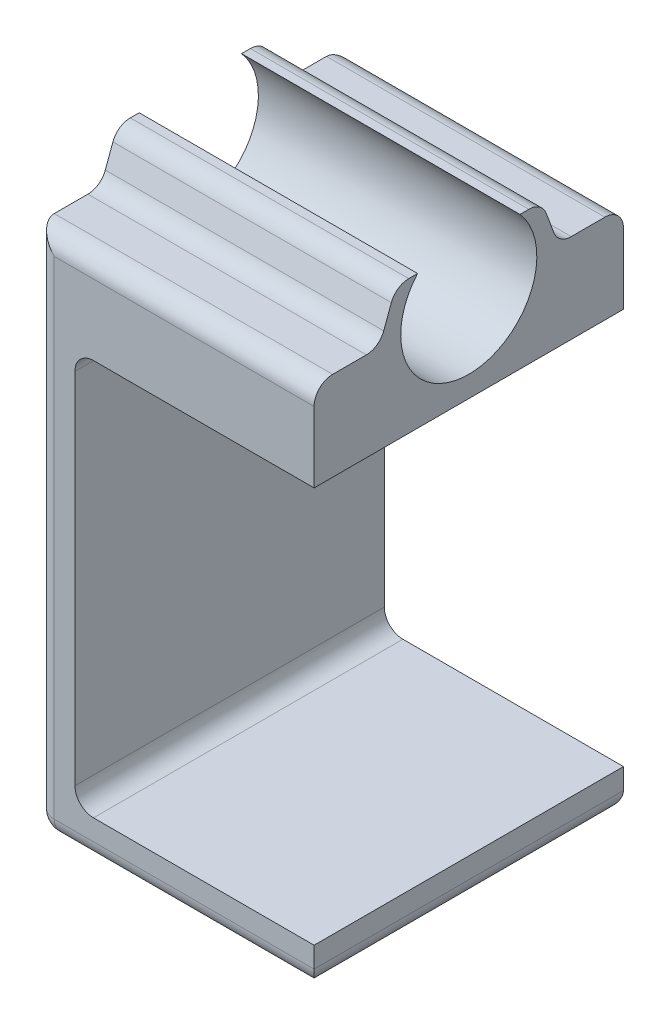
SolidWorks part; units mm, degrees
ref_plane "Front Plane" through (0, 0, 0) normal (0, 0, 1) x (1, 0, 0)
ref_plane "Top Plane" through (0, 0, 0) normal (0, 1, 0) x (1, 0, 0)
ref_plane "Right Plane" through (0, 0, 0) normal (1, 0, 0) x (0, 0, -1)
sketch "Sketch1" plane through (0, 0, 0) normal (0, 1, 0) x (1, 0, 0)
  line L1 (-22.5, -25) -> (22.5, -25)
  line L2 (-22.5, -25) -> (-22.5, 25)
  line L3 (-22.5, 25) -> (22.5, 25)
  line L4 (22.5, -25) -> (22.5, 25)
  line L5 (-22.5, -25) -> (22.5, 25) construction
  line L6 (-22.5, 25) -> (22.5, -25) construction
  point P0 (0, 0)
  dimension "D1" = 45
  dimension "D2" = 50
extrude "Boss-Extrude1" add sketch "Sketch1" along normal blind 92
sketch "Sketch2" plane through (0, 0, -25) normal (0, 0, -1) x (-1, 0, 0)
  line L0 (-22.5, 92) -> (-22.5, 0) construction
  line L1 (-22.5, 6.35) -> (16.15, 6.35)
  line L2 (-22.5, 6.35) -> (-22.5, 70.35)
  line L3 (-22.5, 70.35) -> (16.15, 70.35)
  line L4 (16.15, 6.35) -> (16.15, 70.35)
  line L5 (-22.5, 0) -> (22.5, 0) construction
  line L6 (22.5, 92) -> (22.5, 0) construction
  dimension "D1" = 6.35
  dimension "D2" = 6.35
  dimension "D3" = 64
extrude "Cut-Extrude1" cut sketch "Sketch2" against normal up to surface (50 mm away) up to face at (0, 46, 25)
sketch "Sketch3" plane through (22.5, 0, 0) normal (1, 0, 0) x (0, 0, -1)
  line L0 (0, 92) -> (0, 77.5) construction
  line L1 (-25, 92) -> (25, 92) construction
  circle A0 centre (0, 84.75) radius 11
  dimension "D1" = 22
  dimension "D2" = 7.25
extrude "Cut-Extrude2" cut sketch "Sketch3" against normal up to surface (45 mm away) up to face at (-22.5, 46, 0)
fillet "Fillet1" radius 3 2 edges at (-16.15, 6.35, 0) (-16.15, 70.35, 0)
sketch "Sketch4" plane through (22.5, 0, 0) normal (1, 0, 0) x (0, 0, -1)
  line L0 (11.793, 92) -> (14.47, 84.75)
  line L1 (25, 92) -> (25, 70.35) construction
  line L2 (25, 84.75) -> (-25, 84.75) construction
  line L3 (-25, 92) -> (-25, 70.35) construction
  line L4 (8.2727, 92) -> (25, 92) construction
  line L5 (14.47, 84.75) -> (25, 84.75)
  line L6 (25, 84.75) -> (25, 92)
  line L7 (25, 92) -> (11.793, 92)
  line L8 (0, 84.75) -> (0, 92) construction
  line L9 (-25, 84.75) -> (-25, 92)
  line L10 (-14.47, 84.75) -> (-25, 84.75)
  line L11 (-11.793, 92) -> (-14.47, 84.75)
  line L12 (-25, 92) -> (-11.793, 92)
extrude "Cut-Extrude3" cut sketch "Sketch4" against normal up to surface (45 mm away) up to face at (-22.5, 58.2917, 0)
fillet "Fillet5" radius 3 4 edges at (0, 84.75, 14.47) (0, 92, 11.793) (0, 84.75, -14.47) (0, 92, -11.793)
fillet "Fillet6" radius 3 8 edges at (22.5, 0, 0) (0, 0, -25) (0, 0, 25) (-22.5, 0, 0) (0, 84.75, -25) (0, 84.75, 25) (-22.5, 42.375, 25) (-22.5, 42.375, -25)
sketch "Sketch5" plane through (-22.5, 0, 0) normal (-1, 0, 0) x (0, 0, 1)
  line L0 (-19.5199, 8.015) -> (19.2476, 8.015) construction
  text T0 "OneChair V0.2"
  point P2 (19.2476, 9.4676)
  point P3 (-19.5199, 8.015)
extrude "Cut-Extrude4" cut sketch "Sketch5" against normal blind 1
sketch "Sketch15" plane through (-22.5, 0, 0) normal (-1, 0, 0) x (0, 0, 1)
  line L3 (10.2596, 32.0046) -> (9.9115, 31.8204)
  line L7 (10.2596, 30.9578) -> (10.2596, 30.6198)
  line L10 (12.867, 34.9608) -> (4.2649, 30.6858)
  line L11 (14.52, 34.2529) -> (10.2596, 32.0046)
  line L12 (10.2596, 32.0046) -> (9.9115, 31.8204)
  line L13 (9.9115, 31.8204) -> (-14.2582, 18.9772)
  line L14 (-11.8535, 18.0077) -> (-8.8687, 18.0077)
  line L15 (10.2596, 30.0222) -> (10.2596, 30.9578)
  line L16 (10.828, 30.7106) -> (10.828, 30.7064)
  spline S7 degree 3 poles (-15.2979, 21.0019) (-15.3375, 21.2141) (-15.3567, 21.4299) (-15.3849, 21.6442) knots 29 29 29 29 30 30 30 30
  spline S8 degree 3 poles (-15.1435, 20.3562) (-15.1984, 20.5822) (-15.2583, 20.7902) (-15.2979, 21.0019) knots 28 28 28 28 29 29 29 29
  spline S9 degree 3 poles (-10.0647, 23.0588) (-11.7426, 22.1659) (-13.4314, 21.2673) (-15.1435, 20.3562) knots 27 27 27 27 28 28 28 28
  spline S10 degree 3 poles (-10.1505, 23.6586) (-10.1362, 23.4613) (-10.0952, 23.2658) (-10.0647, 23.0588) knots 26 26 26 26 27 27 27 27
  spline S11 degree 3 poles (-10.0043, 24.7775) (-10.1119, 24.4127) (-10.1781, 24.0401) (-10.1505, 23.6586) knots 25 25 25 25 26 26 26 26
  spline S12 degree 3 poles (-9.1188, 27.7673) (-9.4119, 26.7701) (-9.7102, 25.7744) (-10.0043, 24.7775) knots 24 24 24 24 25 25 25 25
  spline S13 degree 3 poles (-8.585, 28.698) (-8.8238, 28.4241) (-9.0148, 28.1212) (-9.1188, 27.7673) knots 23 23 23 23 24 24 24 24
  spline S14 degree 3 poles (-6.5207, 30.0144) (-7.3559, 29.8102) (-8.0265, 29.3386) (-8.585, 28.698) knots 22 22 22 22 23 23 23 23
  spline S15 degree 3 poles (-5.8867, 30.0896) (-6.0986, 30.0862) (-6.3152, 30.0646) (-6.5207, 30.0144) knots 21 21 21 21 22 22 22 22
  spline S16 degree 3 poles (-3.9427, 30.0956) (-4.5907, 30.095) (-5.2388, 30.0998) (-5.8867, 30.0896) knots 20 20 20 20 21 21 21 21
  spline S17 degree 3 poles (0.0807, 30.0993) (-1.2605, 30.097) (-2.6016, 30.0969) (-3.9427, 30.0956) knots 19 19 19 19 20 20 20 20
  spline S18 degree 3 poles (2.8334, 30.103) (1.916, 30.114) (0.9983, 30.1009) (0.0807, 30.0993) knots 18 18 18 18 19 19 19 19
  spline S19 degree 3 poles (3.4965, 30.2699) (3.284, 30.1558) (3.0781, 30.1) (2.8334, 30.103) knots 17 17 17 17 18 18 18 18
  spline S28 degree 3 poles (-12.5035, 30.7783) (-11.8211, 31.7697) (-10.94, 32.5326) (-9.8566, 33.0581) knots 5 5 5 5 6 6 6 6
  spline S29 degree 3 poles (-13.5209, 28.6858) (-13.2999, 29.4445) (-12.9836, 30.15) (-12.5035, 30.7783) knots 4 4 4 4 5 5 5 5
  spline S30 degree 3 poles (-15.205, 22.9992) (-14.6499, 24.8966) (-14.074, 26.7879) (-13.5209, 28.6858) knots 3 3 3 3 4 4 4 4
  spline S31 degree 3 poles (-15.3675, 22.092) (-15.3147, 22.3949) (-15.2907, 22.706) (-15.205, 22.9992) knots 2 2 2 2 3 3 3 3
  spline S32 degree 3 poles (-15.3849, 22.0015) (-15.3791, 22.0317) (-15.3728, 22.0618) (-15.3675, 22.092) knots 1 1 1 1 2 2 2 2
  spline S33 degree 3 poles (-15.3849, 21.6442) (-15.3849, 21.7633) (-15.3849, 21.8824) (-15.3849, 22.0015) knots 0 0 0 0 1 1 1 1
  spline S35 degree 3 poles (9.9115, 31.8204) (1.8611, 27.5421) (-6.186, 23.2664) (-14.2582, 18.9772) knots 3 3 3 3 4 4 4 4
  spline S36 degree 3 poles (-14.2582, 18.9772) (-14.0985, 18.8485) (-13.9614, 18.7241) (-13.8109, 18.6198) knots 4 4 4 4 5 5 5 5
  spline S37 degree 3 poles (-13.8109, 18.6198) (-13.2728, 18.2448) (-12.6632, 18.08) (-12.0175, 18.0287) knots 5 5 5 5 6 6 6 6
  spline S38 degree 3 poles (-12.0175, 18.0287) (-11.9629, 18.0245) (-11.9082, 18.0144) (-11.8535, 18.0077) knots 6 6 6 6 7 7 7 7
  spline S39 degree 3 poles (-15.3849, 21.6442) (-15.3563, 21.4298) (-15.3378, 21.2137) (-15.2975, 21.0018) knots 9 9 9 9 10 10 10 10
  spline S40 degree 3 poles (-15.2975, 21.0018) (-15.258, 20.7899) (-15.1983, 20.5822) (-15.1436, 20.3561) knots 10 10 10 10 11 11 11 11
  spline S41 degree 3 poles (-15.1436, 20.3561) (-13.4317, 21.2675) (-11.7426, 22.1663) (-10.0643, 23.0584) knots 11 11 11 11 12 12 12 12
  spline S42 degree 3 poles (-10.0643, 23.0584) (-10.0954, 23.2661) (-10.1366, 23.4612) (-10.1501, 23.6588) knots 12 12 12 12 13 13 13 13
  spline S43 degree 3 poles (-10.1501, 23.6588) (-10.1778, 24.0405) (-10.1122, 24.4129) (-10.0046, 24.7779) knots 13 13 13 13 14 14 14 14
  spline S44 degree 3 poles (-10.0046, 24.7779) (-9.7103, 25.7742) (-9.4119, 26.7697) (-9.1184, 27.7669) knots 14 14 14 14 15 15 15 15
  spline S45 degree 3 poles (-9.1184, 27.7669) (-9.015, 28.1209) (-8.8241, 28.4244) (-8.5853, 28.6977) knots 15 15 15 15 16 16 16 16
  spline S46 degree 3 poles (-8.5853, 28.6977) (-8.0262, 29.3384) (-7.3561, 29.8101) (-6.5203, 30.0144) knots 16 16 16 16 17 17 17 17
  spline S47 degree 3 poles (-6.5203, 30.0144) (-6.3152, 30.0648) (-6.0982, 30.0859) (-5.8864, 30.0892) knots 17 17 17 17 18 18 18 18
  spline S48 degree 3 poles (-5.8864, 30.0892) (-5.2389, 30.1002) (-4.5907, 30.0951) (-3.9424, 30.096) knots 18 18 18 18 19 19 19 19
  spline S49 degree 3 poles (-3.9424, 30.096) (-2.6013, 30.0968) (-1.2602, 30.0968) (0.0808, 30.0993) knots 19 19 19 19 20 20 20 20
  spline S50 degree 3 poles (0.0808, 30.0993) (0.9982, 30.101) (1.9163, 30.1144) (2.8336, 30.1027) knots 20 20 20 20 21 21 21 21
  spline S51 degree 3 poles (2.8336, 30.1027) (3.0783, 30.1002) (3.2843, 30.1556) (3.4962, 30.27) knots 21 21 21 21 22 22 22 22
  spline S52 degree 3 poles (3.4962, 30.27) (3.7524, 30.4092) (4.0087, 30.5475) (4.2649, 30.6858) knots 22 22 22 22 23 23 23 23
  spline S62 degree 3 poles (-15.3675, 22.092) (-15.3728, 22.0618) (-15.3791, 22.0317) (-15.3849, 22.0015) knots 9 9 9 9 10 10 10 10
  spline S63 degree 3 poles (-15.205, 22.9992) (-15.2907, 22.706) (-15.3147, 22.3949) (-15.3675, 22.092) knots 8 8 8 8 9 9 9 9
  spline S64 degree 3 poles (-13.5209, 28.6858) (-14.074, 26.7879) (-14.6499, 24.8966) (-15.205, 22.9992) knots 7 7 7 7 8 8 8 8
  spline S65 degree 3 poles (-12.5035, 30.7783) (-12.9836, 30.15) (-13.2999, 29.4445) (-13.5209, 28.6858) knots 6 6 6 6 7 7 7 7
  spline S66 degree 3 poles (-9.8566, 33.0581) (-10.94, 32.5326) (-11.8211, 31.7697) (-12.5035, 30.7783) knots 5 5 5 5 6 6 6 6
  spline S69 degree 3 poles (-8.8687, 18.0077) (-8.8317, 18.0127) (-8.7939, 18.0212) (-8.7569, 18.0212) knots 2 2 2 2 3 3 3 3
  spline S70 degree 3 poles (-8.7569, 18.0212) (-7.4225, 18.0228) (-6.0881, 18.0237) (-4.7538, 18.0254) knots 3 3 3 3 4 4 4 4
  spline S71 degree 3 poles (-4.7538, 18.0254) (-3.3286, 18.027) (-1.9035, 18.0279) (-0.4783, 18.0304) knots 4 4 4 4 5 5 5 5
  spline S72 degree 3 poles (-0.4783, 18.0304) (0.4987, 18.0321) (1.4757, 18.0338) (2.4527, 18.0388) knots 5 5 5 5 6 6 6 6
  spline S73 degree 3 poles (2.4527, 18.0388) (2.9118, 18.0413) (3.344, 18.175) (3.7627, 18.3491) knots 6 6 6 6 7 7 7 7
  spline S74 degree 3 poles (3.7627, 18.3491) (5.2963, 18.9872) (6.5576, 19.9735) (7.5253, 21.3255) knots 7 7 7 7 8 8 8 8
  spline S75 degree 3 poles (7.5253, 21.3255) (7.9466, 21.9132) (8.1921, 22.5808) (8.393, 23.272) knots 8 8 8 8 9 9 9 9
  spline S76 degree 3 poles (8.393, 23.272) (8.7991, 24.6694) (9.2229, 26.0618) (9.6341, 27.4575) knots 9 9 9 9 10 10 10 10
  spline S77 degree 3 poles (9.6341, 27.4575) (9.8098, 28.052) (9.9788, 28.6472) (10.1352, 29.2467) knots 10 10 10 10 11 11 11 11
  spline S78 degree 3 poles (10.1352, 29.2467) (10.1924, 29.4653) (10.2066, 29.6949) (10.2403, 29.9202) knots 11 11 11 11 12 12 12 12
  spline S79 degree 3 poles (10.2403, 29.9202) (10.2453, 29.9505) (10.2529, 29.9799) (10.2596, 30.0102) knots 12 12 12 12 13 13 13 13
  spline S80 degree 3 poles (-3.0486, 22.1503) (-0.3135, 24.0615) (2.4216, 25.9735) (5.1845, 27.9048) knots 8 8 8 8 9 9 9 9
  spline S81 degree 3 poles (-3.0369, 22.1293) (-3.0411, 22.1361) (-3.0444, 22.1428) (-3.0486, 22.1503) knots 7 7 7 7 8 8 8 8
  spline S82 degree 3 poles (-2.9957, 22.1276) (-3.0091, 22.1276) (-3.0234, 22.1285) (-3.0369, 22.1293) knots 6 6 6 6 7 7 7 7
  spline S83 degree 3 poles (1.2899, 22.1361) (-0.1386, 22.1243) (-1.5671, 22.1293) (-2.9957, 22.1276) knots 5 5 5 5 6 6 6 6
  spline S84 degree 3 poles (3.2196, 22.8306) (2.6587, 22.3774) (2.0088, 22.1428) (1.2899, 22.1361) knots 4 4 4 4 5 5 5 5
  spline S85 degree 3 poles (4.057, 24.0926) (3.8897, 23.6016) (3.629, 23.161) (3.2196, 22.8306) knots 3 3 3 3 4 4 4 4
  spline S86 degree 3 poles (4.4757, 25.4572) (4.3395, 25.0015) (4.21, 24.5424) (4.057, 24.0926) knots 2 2 2 2 3 3 3 3
  spline S87 degree 3 poles (5.145, 27.7106) (4.9222, 26.9598) (4.7002, 26.2081) (4.4757, 25.4572) knots 1 1 1 1 2 2 2 2
  spline S88 degree 3 poles (5.1845, 27.9048) (5.1677, 27.8207) (5.1601, 27.7644) (5.145, 27.7106) knots 0 0 0 0 1 1 1 1
  spline S93 degree 3 poles (-9.8566, 33.0581) (-9.2168, 33.6509) (-5.7863, 34.9432) (-4.9354, 35.2913) knots 5 5 5 5 6 6 6 6
  spline S94 degree 3 poles (-4.9354, 35.2913) (-4.0778, 35.6427) (-3.1823, 35.9) (-2.3071, 36.2086) knots 6 6 6 6 7 7 7 7
  spline S95 degree 3 poles (-2.3071, 36.2086) (-2.1599, 36.2607) (-1.9985, 36.3372) (-1.8984, 36.4499) knots 7 7 7 7 8 8 8 8
  spline S96 degree 3 poles (-1.8984, 36.4499) (-0.4228, 38.1197) (1.0444, 39.7972) (2.5124, 41.4729) knots 8 8 8 8 9 9 9 9
  spline S97 degree 3 poles (2.5124, 41.4729) (2.5385, 41.5031) (2.5604, 41.5368) (2.5957, 41.5847) knots 9 9 9 9 10 10 10 10
  spline S98 degree 3 poles (2.5957, 41.5847) (2.5309, 41.6301) (2.4754, 41.6738) (2.4158, 41.7091) knots 10 10 10 10 11 11 11 11
  spline S99 degree 3 poles (2.4158, 41.7091) (1.659, 42.1607) (0.8989, 42.6063) (0.1489, 43.067) knots 11 11 11 11 12 12 12 12
  spline S100 degree 3 poles (0.1489, 43.067) (-0.0091, 43.1637) (-0.0983, 43.1419) (-0.2269, 43.025) knots 12 12 12 12 13 13 13 13
  spline S101 degree 3 poles (-0.2269, 43.025) (-1.2233, 42.1195) (-2.2255, 41.219) (-3.2294, 40.321) knots 13 13 13 13 14 14 14 14
  spline S102 degree 3 poles (-3.2294, 40.321) (-4.1745, 39.476) (-5.6005, 39.687) (-6.1949, 40.7548) knots 14 14 14 14 15 15 15 15
  spline S103 degree 3 poles (-6.1949, 40.7548) (-6.6128, 41.5057) (-6.4665, 42.5155) (-5.8216, 43.0881) knots 15 15 15 15 16 16 16 16
  spline S104 degree 3 poles (-5.8216, 43.0881) (-4.3637, 44.3837) (-2.8788, 45.65) (-1.4351, 46.9616) knots 16 16 16 16 17 17 17 17
  spline S105 degree 3 poles (-1.4351, 46.9616) (-0.9517, 47.4006) (0.117, 47.4703) (0.6484, 47.1441) knots 17 17 17 17 18 18 18 18
  spline S106 degree 3 poles (0.6484, 47.1441) (1.9474, 46.3462) (3.2759, 45.5953) (4.5918, 44.8252) knots 18 18 18 18 19 19 19 19
  spline S107 degree 3 poles (4.5918, 44.8252) (6.1615, 43.9079) (7.7187, 42.9653) (9.307, 42.0816) knots 19 19 19 19 20 20 20 20
  spline S108 degree 3 poles (9.307, 42.0816) (10.2016, 41.583) (10.3933, 40.6615) (10.3025, 39.9687) knots 20 20 20 20 21 21 21 21
  spline S109 degree 3 poles (10.3025, 39.9687) (10.2436, 39.5146) (10.0637, 39.1169) (9.7526, 38.7655) knots 21 21 21 21 22 22 22 22
  spline S110 degree 3 poles (9.7526, 38.7655) (8.6167, 37.4816) (7.495, 36.1851) (6.3692, 34.8936) knots 22 22 22 22 23 23 23 23
  spline S111 degree 3 poles (6.3692, 34.8936) (6.312, 34.828) (6.2582, 34.7591) (6.1657, 34.6464) knots 23 23 23 23 24 24 24 24
  spline S112 degree 3 poles (6.1657, 34.6464) (6.2927, 34.6321) (6.3675, 34.6119) (6.4407, 34.6161) knots 24 24 24 24 25 25 25 25
  spline S113 degree 3 poles (6.4407, 34.6161) (8.5191, 34.7271) (10.5976, 34.8322) (12.6752, 34.9566) knots 25 25 25 25 26 26 26 26
  spline S114 degree 3 poles (12.6752, 34.9566) (12.74, 34.9608) (12.8047, 34.9617) (12.867, 34.9608) knots 26 26 26 26 27 27 27 27
  spline S115 degree 3 poles (14.8496, 33.4566) (14.7857, 33.7627) (14.6738, 34.0301) (14.52, 34.2529) knots 0 0 0 0 1 1 1 1
  spline S116 degree 3 poles (-14.2582, 18.9772) (-14.0985, 18.8485) (-13.9614, 18.7241) (-13.8109, 18.6198) knots 4 4 4 4 5 5 5 5
  spline S117 degree 3 poles (-13.8109, 18.6198) (-13.2728, 18.2448) (-12.6632, 18.08) (-12.0175, 18.0287) knots 5 5 5 5 6 6 6 6
  spline S118 degree 3 poles (-12.0175, 18.0287) (-11.9629, 18.0245) (-11.9082, 18.0144) (-11.8535, 18.0077) knots 6 6 6 6 7 7 7 7
  spline S119 degree 3 poles (-8.8687, 18.0077) (-8.8317, 18.0127) (-8.7939, 18.0212) (-8.7569, 18.0212) knots 8 8 8 8 9 9 9 9
  spline S120 degree 3 poles (-8.7569, 18.0212) (-7.4225, 18.0228) (-6.0881, 18.0237) (-4.7538, 18.0254) knots 9 9 9 9 10 10 10 10
  spline S121 degree 3 poles (-4.7538, 18.0254) (-3.3286, 18.027) (-1.9035, 18.0279) (-0.4783, 18.0304) knots 10 10 10 10 11 11 11 11
  spline S122 degree 3 poles (-0.4783, 18.0304) (0.4987, 18.0321) (1.4757, 18.0338) (2.4527, 18.0388) knots 11 11 11 11 12 12 12 12
  spline S123 degree 3 poles (2.4527, 18.0388) (2.9118, 18.0413) (3.344, 18.175) (3.7627, 18.3491) knots 12 12 12 12 13 13 13 13
  spline S124 degree 3 poles (3.7627, 18.3491) (5.2963, 18.9872) (6.5576, 19.9735) (7.5253, 21.3255) knots 13 13 13 13 14 14 14 14
  spline S125 degree 3 poles (7.5253, 21.3255) (7.9466, 21.9132) (8.1921, 22.5808) (8.393, 23.272) knots 14 14 14 14 15 15 15 15
  spline S126 degree 3 poles (8.393, 23.272) (8.7991, 24.6694) (9.2229, 26.0618) (9.6341, 27.4575) knots 15 15 15 15 16 16 16 16
  spline S127 degree 3 poles (9.6341, 27.4575) (9.8098, 28.052) (9.9788, 28.6472) (10.1352, 29.2467) knots 16 16 16 16 17 17 17 17
  spline S128 degree 3 poles (10.1352, 29.2467) (10.1924, 29.4653) (10.2066, 29.6949) (10.2403, 29.9202) knots 17 17 17 17 18 18 18 18
  spline S129 degree 3 poles (10.2403, 29.9202) (10.2447, 29.9466) (10.251, 29.9722) (10.257, 29.9984) knots 18 18 18 18 19 19 19 19
  spline S130 degree 3 poles (10.257, 29.9984) (10.2587, 30.0062) (10.2596, 30.0142) (10.2596, 30.0222) knots 19 19 19 19 20 20 20 20
  spline S131 degree 3 poles (10.2596, 30.9578) (10.2596, 31.0378) (10.322, 31.1039) (10.4019, 31.1082) knots 21 21 21 21 22 22 22 22
  spline S132 degree 3 poles (10.4019, 31.1082) (10.4037, 31.1083) (10.4055, 31.1084) (10.4073, 31.1085) knots 22 22 22 22 23 23 23 23
  spline S133 degree 3 poles (10.4073, 31.1085) (10.6357, 31.1211) (10.828, 30.9394) (10.828, 30.7106) knots 23 23 23 23 24 24 24 24
  spline S134 degree 3 poles (10.828, 30.7064) (10.7683, 29.9169) (10.7078, 29.1282) (10.6481, 28.3387) knots 25 25 25 25 26 26 26 26
  spline S135 degree 3 poles (10.6481, 28.3387) (10.527, 26.7109) (10.416, 25.0822) (10.2798, 23.4561) knots 26 26 26 26 27 27 27 27
  spline S136 degree 3 poles (10.2798, 23.4561) (10.2277, 22.8331) (10.453, 22.3193) (10.8734, 21.9132) knots 27 27 27 27 28 28 28 28
  spline S137 degree 3 poles (10.8734, 21.9132) (11.8689, 20.9514) (13.6792, 21.4987) (13.9718, 22.8491) knots 28 28 28 28 29 29 29 29
  spline S138 degree 3 poles (13.9718, 22.8491) (14.0752, 23.3241) (14.0844, 23.8202) (14.1248, 24.307) knots 29 29 29 29 30 30 30 30
  spline S139 degree 3 poles (14.1248, 24.307) (14.2492, 25.7952) (14.3661, 27.2843) (14.488, 28.7725) knots 30 30 30 30 31 31 31 31
  spline S140 degree 3 poles (14.488, 28.7725) (14.6099, 30.2608) (14.7344, 31.749) (14.8563, 33.238) knots 31 31 31 31 32 32 32 32
  spline S141 degree 3 poles (14.8563, 33.238) (14.8622, 33.3103) (14.8639, 33.386) (14.8496, 33.4566) knots 32 32 32 32 33 33 33 33
  spline S142 degree 3 poles (4.057, 24.0926) (3.8897, 23.6016) (3.629, 23.161) (3.2196, 22.8306) knots 8 8 8 8 9 9 9 9
  spline S143 degree 3 poles (4.4757, 25.4572) (4.3395, 25.0015) (4.21, 24.5424) (4.057, 24.0926) knots 7 7 7 7 8 8 8 8
  spline S144 degree 3 poles (5.145, 27.7106) (4.9222, 26.9598) (4.7002, 26.2081) (4.4757, 25.4572) knots 6 6 6 6 7 7 7 7
  spline S145 degree 3 poles (5.1845, 27.9048) (5.1677, 27.8207) (5.1601, 27.7644) (5.145, 27.7106) knots 5 5 5 5 6 6 6 6
  spline S146 degree 3 poles (-3.0486, 22.1503) (-0.3135, 24.0615) (2.4216, 25.9735) (5.1845, 27.9048) knots 4 4 4 4 5 5 5 5
  spline S147 degree 3 poles (-3.0369, 22.1293) (-3.0411, 22.1361) (-3.0444, 22.1428) (-3.0486, 22.1503) knots 3 3 3 3 4 4 4 4
  spline S148 degree 3 poles (-2.9957, 22.1276) (-3.0091, 22.1276) (-3.0234, 22.1285) (-3.0369, 22.1293) knots 2 2 2 2 3 3 3 3
  spline S149 degree 3 poles (1.2899, 22.1361) (-0.1386, 22.1243) (-1.5671, 22.1293) (-2.9957, 22.1276) knots 1 1 1 1 2 2 2 2
  spline S150 degree 3 poles (3.2196, 22.8306) (2.6587, 22.3774) (2.0088, 22.1428) (1.2899, 22.1361) knots 0 0 0 0 1 1 1 1
  spline S158 degree 3 poles (7.5381, 45.8286) (7.5373, 47.5059) (9.0149, 48.9528) (10.725, 48.9493) knots 3 3 3 3 4 4 4 4
  spline S159 degree 3 poles (10.7155, 42.5606) (8.9098, 42.5606) (7.539, 43.9705) (7.5381, 45.8286) knots 2 2 2 2 3 3 3 3
  spline S160 degree 3 poles (13.8947, 45.7198) (13.8872, 44.0064) (12.4322, 42.5606) (10.7155, 42.5606) knots 1 1 1 1 2 2 2 2
  spline S161 degree 3 poles (10.725, 48.9493) (12.4988, 48.9457) (13.9025, 47.5155) (13.8947, 45.7198) knots 0 0 0 0 1 1 1 1
  point P0 (17714.6066, -15032.0985)
  point P1 (0, 0)
  point P2 (0, 0)
  point P3 (0, 0)
extrude "Cut-Extrude6" cut sketch "Sketch15" against normal blind 1 contours S114 S113 S112 S111 S110 S109 S108 S107 S106 S105 S104 S103 S102 S101 S100 S99 S98 S97 S96 S95 S94 S93 S28 S29 S30 S31 S32 S33 S39 S7 S40 S8 S9 S41 S10 S42 S11 S43 S44 S12 S13 S45 S46 S14 S15 S16 | S161 S158 S159 S160 | S140 S141 S115 L11 L3 S35 S36 S37 S38 L14 S69 S70 S71 S72 S73 S74 S75 S76 S77 S78 S79 S130 L15 L7 S131 S132 S133 L16 S134 S135 S136 S137 S138 S139 S80 S88 S87 S86 S85 S84 S83 S82 S81
